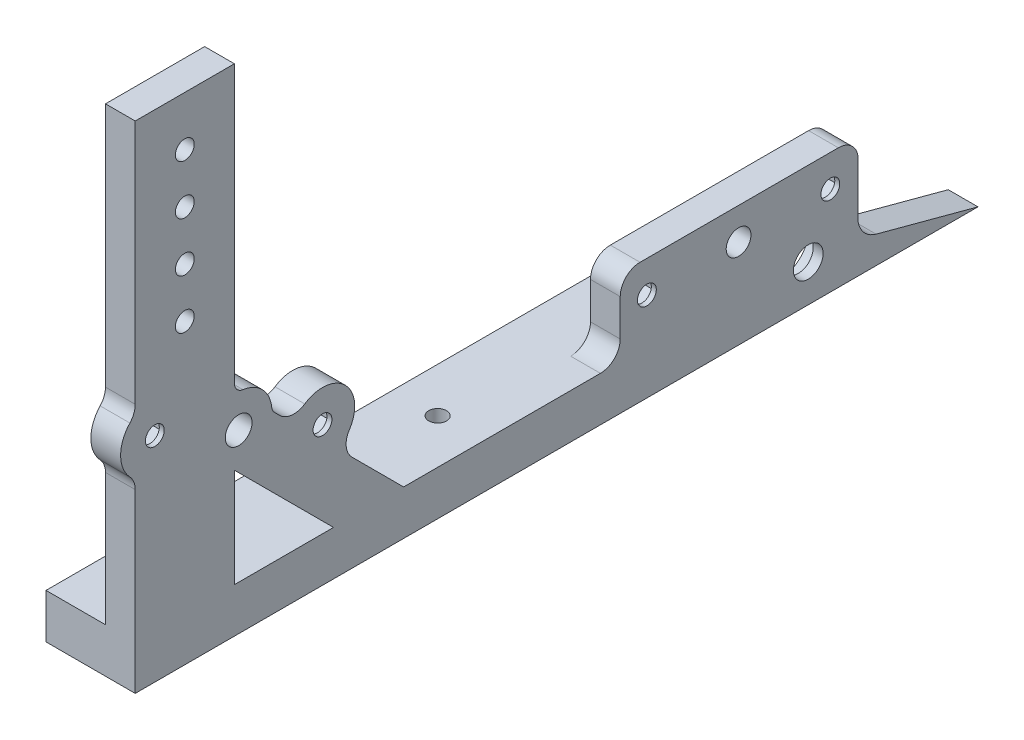
SolidWorks part; units mm, degrees
ref_plane "Front Plane" through (0, 0, 0) normal (0, 0, 1) x (1, 0, 0)
ref_plane "Top Plane" through (0, 0, 0) normal (0, 1, 0) x (1, 0, 0)
ref_plane "Right Plane" through (0, 0, 0) normal (1, 0, 0) x (0, 0, -1)
sketch "Sketch1" plane through (0, 0, 0) normal (1, 0, 0) x (0, 0, -1)
  line L0 (0, 0) -> (127, 0)
  line L1 (127, 0) -> (100.9008, 6.9932)
  line L2 (0, 11.43) -> (40.8104, 11.43) construction
  line L3 (0, 11.43) -> (0, 0) construction
  line L4 (0, 11.43) -> (-20.1395, 11.43)
  line L5 (-88.9, 127) -> (-88.9, 64.1493)
  line L6 (-88.9, 0) -> (0, 0)
  line L7 (-76.2, 127) -> (-76.2, 0) construction
  line L8 (65.6713, 22.86) -> (83.5147, 9.525) construction
  line L9 (70.1065, 31.2894) -> (89.5762, 21.0452) construction
  line L10 (-88.9, 127) -> (-63.5, 127)
  line L11 (-63.5, 11.43) -> (-63.5, 36.83)
  line L12 (58.4401, 29.0597) -> (40.8104, 11.43) construction
  line L13 (-63.5, 36.83) -> (-38.1, 11.43)
  line L14 (-62.4025, 45.1562) -> (65.6713, 22.86) construction
  line L15 (-38.1, 11.43) -> (-63.5, 11.43)
  line L16 (-53.2084, 44.4989) -> (-51.8709, 43.1614)
  line L17 (-62.4025, 45.1562) -> (-14.8305, 401.9992) construction
  line L18 (-63.5, 56.1106) -> (-63.5, 127)
  line L19 (-88.9, 0) -> (-88.9, 47.5016) construction
  line L20 (-88.9, 401.9992) -> (-14.8305, 401.9992) construction
  line L21 (42.1763, 22.86) -> (89.1663, 22.86) construction
  line L22 (35.3451, 16.51) -> (35.3451, 25.9159)
  line L23 (-88.9, 0) -> (-88.9, 47.5016) construction
  line L24 (40.4251, 30.9959) -> (91.2251, 30.9959)
  line L25 (96.3051, 25.9159) -> (96.3051, 11.9459)
  line L26 (0, 11.43) -> (30.2651, 11.43)
  line L27 (-83.8791, 54.6836) -> (-40.9259, 35.6289) construction
  line L28 (-33.3933, 24.6839) -> (-20.1395, 11.43)
  line L29 (-88.9, 45.2178) -> (-88.9, 0)
  line L30 (-88.9, 61.8655) -> (-88.9, 401.9992) construction
  line L31 (-88.9, 61.8655) -> (-88.9, 109.7039) construction
  circle A0 centre (83.5147, 9.525) radius 7.9375
  arc A1 (96.3051, 11.9459) -> (89.5762, 21.0452) centre (83.5147, 9.525) ccw construction
  circle A2 centre (83.5147, 9.525) radius 6.35 construction
  arc A3 (70.1065, 31.2894) -> (58.4401, 29.0597) centre (65.6713, 22.86) ccw construction
  arc A4 (96.3051, 11.9459) -> (100.9008, 6.9932) centre (102.5443, 13.1269) ccw
  circle A5 centre (-76.2, 114.3) radius 2.413
  circle A6 centre (-76.2, 88.9) radius 2.413
  circle A7 centre (-76.2, 101.6) radius 2.413
  circle A8 centre (-76.2, 76.2) radius 2.413
  circle A9 centre (65.6713, 22.86) radius 3.175
  circle A10 centre (-62.4025, 45.1562) radius 3.429
  arc A11 (-53.9388, 46.0331) -> (-61.2916, 53.5924) centre (-62.4025, 45.1562) ccw
  arc A12 (-63.5, 56.1106) -> (-61.2916, 53.5924) centre (-60.96, 56.1106) ccw
  circle A13 centre (-14.8305, 401.9992) radius 22.225 construction
  arc A14 (-53.2084, 44.4989) -> (-53.9388, 46.0331) centre (-51.4123, 46.2949) cw
  circle A15 centre (42.1763, 22.86) radius 2.413
  circle A16 centre (89.1663, 22.86) radius 2.413
  circle A17 centre (65.6713, 22.86) radius 16.002 construction
  arc A18 (96.3051, 25.9159) -> (91.2251, 30.9959) centre (91.2251, 25.9159) ccw
  arc A19 (40.4251, 30.9959) -> (35.3451, 25.9159) centre (40.4251, 25.9159) ccw
  arc A20 (35.3451, 16.51) -> (30.2651, 11.43) centre (30.2651, 16.51) cw
  circle A21 centre (-83.8791, 54.6836) radius 2.413
  circle A22 centre (-40.9259, 35.6289) radius 2.413
  circle A23 centre (-62.4025, 45.1562) radius 16.002 construction
  arc A24 (-34.0392, 31.0771) -> (-45.4777, 42.5155) centre (-40.9259, 35.6289) ccw
  arc A25 (-33.3933, 24.6839) -> (-34.0392, 31.0771) centre (-29.8012, 28.276) cw
  arc A26 (-51.8709, 43.1614) -> (-45.4777, 42.5155) centre (-48.2788, 46.7535) ccw
  arc A27 (-90.2732, 60.6756) -> (-90.2732, 48.6915) centre (-83.8791, 54.6836) ccw
  arc A28 (-88.9, 45.2178) -> (-90.2732, 48.6915) centre (-93.98, 45.2178) ccw
  arc A29 (-90.2732, 60.6756) -> (-88.9, 64.1493) centre (-93.98, 64.1493) ccw
  point P6 (83.5147, 1.5875)
  point P49 (65.6713, 22.86)
  point P58 (96.3051, 30.9959)
  point P61 (35.3451, 30.9959)
  point P64 (35.3451, 11.43)
  point P67 (-62.4025, 45.1562)
  point P75 (-37.0499, 28.3404)
  dimension "D1" = 15.875
  dimension "D2" = 1.5875
  dimension "D3" = 5.08
  dimension "D7" = 12.7
  dimension "D8" = 360
  dimension "D9" = 6.35
  dimension "D13" = 4.826
  dimension "D15" = 25.4
  dimension "D17" = 12.7
  dimension "D18" = 11.9459
  dimension "D19" = 6.35
  dimension "D22" = 31.2894
  dimension "D28" = 5.08
  dimension "D29" = 25.4
  dimension "D34" = 44.45
  dimension "D30" = 6.858
  dimension "D35" = 2.54
  dimension "D33" = 4.826
  dimension "D38" = 32.004
  dimension "D41" = 5.08
  dimension "D43" = 32.004
  dimension "D44" = 16.51
  dimension "D45" = 5.08
  dimension "D46" = 6.35
  dimension "D47" = 5.08
  dimension "D4" = 127
  dimension "D5" = 15
  dimension "D6" = 11.43
  dimension "D10" = 215.9
  dimension "D11" = 25.4
  dimension "D12" = 127
  dimension "D14" = 12.7
  dimension "D16" = 12.7
  dimension "D20" = 22.2758
  dimension "D21" = 22.86
  dimension "D23" = 45
  dimension "D24" = 24.9322
  dimension "D25" = 130
  dimension "D26" = 45
  dimension "D27" = 25.4
  dimension "D31" = 12.7
  dimension "D32" = 46.99
  dimension "D36" = 401.9992
  dimension "D37" = 74.0695
  dimension "D39" = 19.05
  dimension "D40" = 60.96
  dimension "D42" = 46.99
extrude "Boss-Extrude1" add sketch "Sketch1" along normal blind 7.62
sketch "Sketch2" plane through (7.62, 0, 0) normal (1, 0, 0) x (0, 0, -1)
  circle A0 centre (83.5147, 9.525) radius 7.9375 construction
  circle A1 centre (83.5147, 9.525) radius 3.81
  circle A2 centre (83.5147, 9.525) radius 7.9375
  dimension "D1" = 7.62
extrude "Boss-Extrude2" add sketch "Sketch2" against normal blind 2.54
sketch "Sketch3" plane through (0, 0, 0) normal (-1, 0, 0) x (0, 0, 1)
  line L0 (88.9, 0) -> (-127, 0) construction
  line L1 (88.9, 11.43) -> (-66.04, 11.43)
  line L2 (88.9, 11.43) -> (88.9, 0)
  line L3 (88.9, 0) -> (-66.04, 0)
  line L4 (-66.04, 11.43) -> (-66.04, 0)
  line L5 (88.9, 0) -> (-127, 0) construction
  line L6 (88.9, 127) -> (88.9, 64.1493) construction
  line L7 (-30.2651, 11.43) -> (20.1395, 11.43) construction
  dimension "D1" = 154.94
extrude "Boss-Extrude3" add sketch "Sketch3" along normal blind 15.24
fillet "Fillet1" radius 5.08 1 edges at (0, 5.715, -66.04)
sketch "Sketch5" plane through (0, 0, 0) normal (0, -1, 0) x (1, 0, 0)
  line L0 (7.62, -127) -> (-15.24, -127) construction
  line L1 (-15.24, -127) -> (-15.24, -66.04) construction
  line L2 (-3.81, -127) -> (-3.81, -50.8) construction
  circle A0 centre (-3.81, -50.8) radius 2.286
  circle A1 centre (-3.81, 0) radius 2.286
  dimension "D2" = 4.572
  dimension "D1" = 76.2
  dimension "D3" = 2
extrude "Cut-Extrude1" cut sketch "Sketch5" against normal through all
sketch "Sketch6" plane through (0, 0, 0) normal (0, -1, 0) x (1, 0, 0)
  line L0 (7.62, -127) -> (0, -127) construction
  line L1 (1.6159, -50.8) -> (-1.097, -46.101)
  line L2 (-1.097, -46.101) -> (-6.523, -46.101)
  line L3 (-6.523, -46.101) -> (-9.2359, -50.8)
  line L4 (-9.2359, -50.8) -> (-6.523, -55.499)
  line L5 (-6.523, -55.499) -> (-1.097, -55.499)
  line L6 (-1.097, -55.499) -> (1.6159, -50.8)
  line L7 (-1.097, -4.699) -> (1.6159, 0)
  line L8 (1.6159, 0) -> (-1.097, 4.699)
  line L9 (-1.097, 4.699) -> (-6.523, 4.699)
  line L10 (-6.523, 4.699) -> (-9.2359, 0)
  line L11 (-9.2359, 0) -> (-6.523, -4.699)
  line L12 (-6.523, -4.699) -> (-1.097, -4.699)
  circle A0 centre (-3.81, -50.8) radius 4.699 construction
  circle A1 centre (-3.81, 0) radius 4.699 construction
  dimension "D1" = 9.398
extrude "Cut-Extrude2" cut sketch "Sketch6" against normal blind 6.35
sketch "Sketch7" plane through (0, 0, 0) normal (-1, 0, 0) x (0, 0, 1)
  line L0 (-35.3451, 25.9159) -> (-35.3451, 16.51) construction
  line L1 (-84.4673, 25.573) -> (-89.1663, 28.2859)
  line L2 (-89.1663, 28.2859) -> (-93.8653, 25.573)
  line L3 (-93.8653, 25.573) -> (-93.8653, 20.147)
  line L4 (-93.8653, 20.147) -> (-89.1663, 17.4341)
  line L5 (-89.1663, 17.4341) -> (-84.4673, 20.147)
  line L6 (-84.4673, 20.147) -> (-84.4673, 25.573)
  line L7 (-37.4773, 25.573) -> (-42.1763, 28.2859)
  line L8 (-42.1763, 28.2859) -> (-46.8753, 25.573)
  line L9 (-46.8753, 25.573) -> (-46.8753, 20.147)
  line L10 (-46.8753, 20.147) -> (-42.1763, 17.4341)
  line L11 (-42.1763, 17.4341) -> (-37.4773, 20.147)
  line L12 (-37.4773, 20.147) -> (-37.4773, 25.573)
  line L14 (45.6249, 38.3418) -> (40.9259, 41.0548)
  line L15 (40.9259, 41.0548) -> (36.2269, 38.3418)
  line L16 (36.2269, 38.3418) -> (36.2269, 32.9159)
  line L17 (36.2269, 32.9159) -> (40.9259, 30.2029)
  line L18 (40.9259, 30.2029) -> (45.6249, 32.9159)
  line L19 (45.6249, 32.9159) -> (45.6249, 38.3418)
  line L20 (88.5781, 57.3965) -> (83.8791, 60.1095)
  line L21 (83.8791, 60.1095) -> (79.1801, 57.3965)
  line L22 (79.1801, 57.3965) -> (79.1801, 51.9706)
  line L23 (79.1801, 51.9706) -> (83.8791, 49.2576)
  line L24 (83.8791, 49.2576) -> (88.5781, 51.9706)
  line L25 (88.5781, 51.9706) -> (88.5781, 57.3965)
  line L26 (88.9, 127) -> (88.9, 64.1493) construction
  circle A0 centre (-89.1663, 22.86) radius 4.699 construction
  circle A1 centre (-42.1763, 22.86) radius 4.699 construction
  circle A2 centre (40.9259, 35.6289) radius 4.699 construction
  circle A3 centre (83.8791, 54.6836) radius 4.699 construction
  dimension "D1" = 9.398
extrude "Cut-Extrude3" cut sketch "Sketch7" against normal blind 6.35
